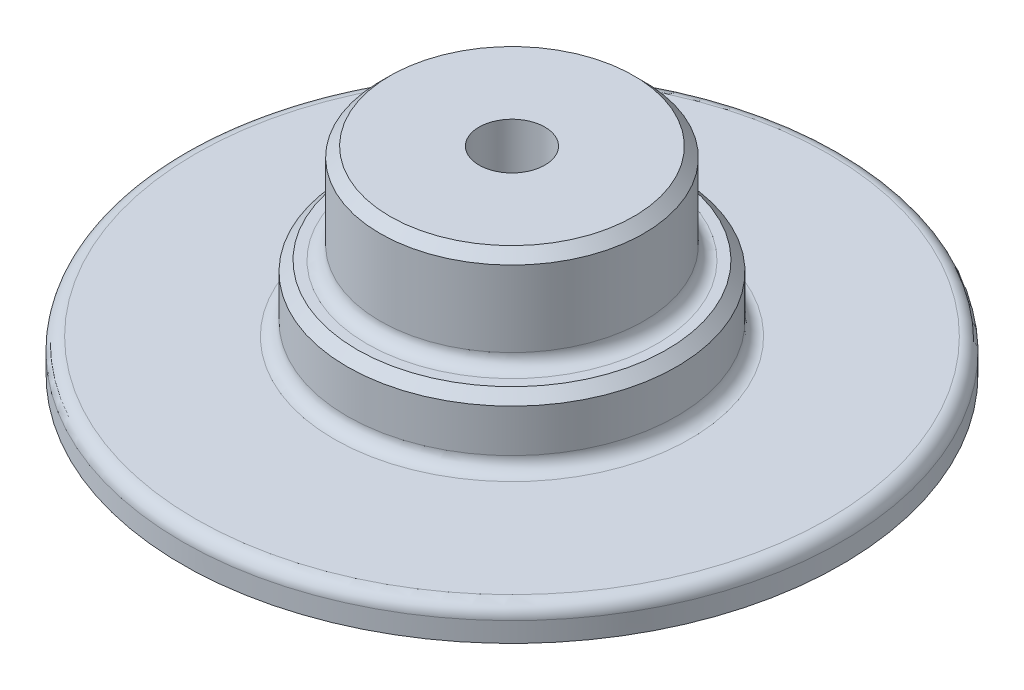
SolidWorks part; units mm, degrees
ref_plane "Front" through (0, 0, 0) normal (0, 0, 1) x (1, 0, 0)
ref_plane "Top" through (0, 0, 0) normal (0, 1, 0) x (1, 0, 0)
ref_plane "Right" through (0, 0, 0) normal (1, 0, 0) x (0, 0, -1)
sketch "Sketch1" plane through (0, 0, 0) normal (0, 0, 1) x (1, 0, 0)
  line L0 (180, 0) -> (0, 0)
  line L1 (0, 0) -> (0, 120)
  line L2 (0, 120) -> (60, 120)
  line L3 (60, 120) -> (60, 60)
  line L4 (60, 60) -> (80, 60)
  line L5 (80, 60) -> (80, 20)
  line L6 (80, 20) -> (180, 20)
  line L7 (180, 20) -> (180, 0)
  line L8 (-20, 0) -> (-20, 120) construction
  dimension "D1" = 120
  dimension "D2" = 20
  dimension "D3" = 40
  dimension "D4" = 60
  dimension "D5" = 20
  dimension "D6" = 180
  dimension "D7" = 20
revolve "Revolve5" add sketch "Sketch1" angle 360 about L8
fillet "Fillet4" radius 8 1 edges at (-20, 20, -200)
chamfer "Chamfer5" distance 6 angle 45 2 edges at (-20, 120, -80) (-20, 60, -100)
fillet "Fillet5" radius 8 2 edges at (-20, 60, -80) (-20, 20, -100)
